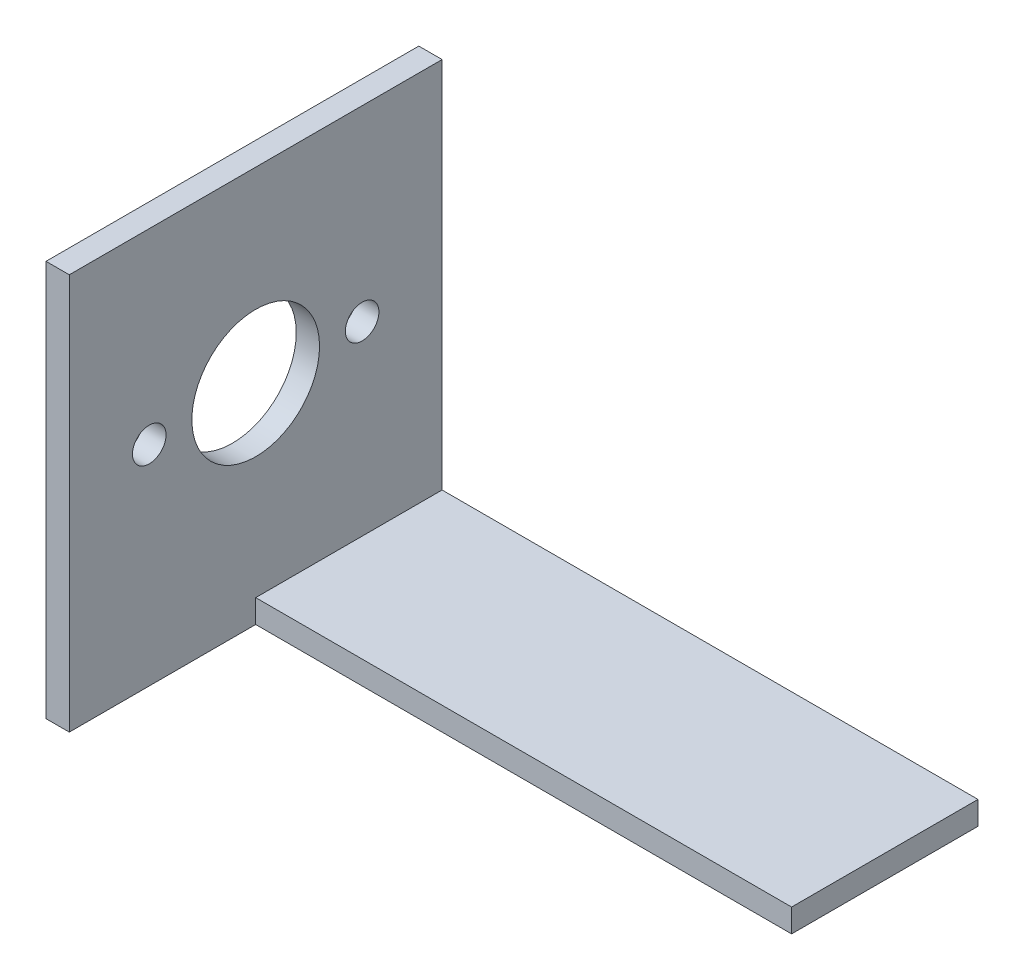
SolidWorks part; units mm, degrees
ref_plane "Front Plane" through (0, 0, 0) normal (0, 0, 1) x (1, 0, 0)
ref_plane "Top Plane" through (0, 0, 0) normal (0, 1, 0) x (1, 0, 0)
ref_plane "Right Plane" through (0, 0, 0) normal (1, 0, 0) x (0, 0, -1)
sketch "Sketch1" plane through (0, 0, 0) normal (0, 1, 0) x (1, 0, 0)
  line L1 (0, 0) -> (76.2, 0)
  line L2 (0, 0) -> (0, 50.8)
  line L3 (0, 50.8) -> (76.2, 50.8)
  line L4 (76.2, 0) -> (76.2, 50.8)
  dimension "D1" = 50.8
  dimension "D2" = 76.2
extrude "Boss-Extrude1" add sketch "Sketch1" along normal blind 3.175
sketch "Sketch2" plane through (0, 0, 0) normal (-1, 0, 0) x (0, 0, 1)
  line L0 (0, 3.175) -> (0, 0) construction
  line L1 (-50.8, 0) -> (0, 0)
  line L2 (-50.8, 0) -> (-50.8, 53.975)
  line L3 (-50.8, 53.975) -> (0, 53.975)
  line L4 (0, 0) -> (0, 53.975)
  dimension "D1" = 53.975
extrude "Boss-Extrude2" add sketch "Sketch2" against normal blind 3.175
sketch "Sketch4" plane through (3.175, 0, 0) normal (1, 0, 0) x (0, 0, -1)
  line L0 (25.4, 53.975) -> (25.4, 3.175) construction
  line L1 (0, 53.975) -> (50.8, 53.975) construction
  line L2 (50.8, 3.175) -> (0, 3.175) construction
  line L3 (0, 3.175) -> (50.8, 3.175) construction
  circle A0 centre (10.8966, 28.4988) radius 2.286
  circle A1 centre (39.9034, 28.4988) radius 2.286
  circle A2 centre (25.4, 28.4988) radius 8.6995
  dimension "D2" = 4.572
  dimension "D4" = 17.399
  dimension "D1" = 29.0068
  dimension "D3" = 25.3238
extrude "Cut-Extrude2" cut sketch "Sketch4" against normal blind 3.175
sketch "Sketch6" plane through (0, 3.175, 0) normal (0, 1, 0) x (1, 0, 0)
  line L0 (76.2, 0) -> (76.2, 50.8) construction
  line L1 (3.175, 0) -> (76.2, 0)
  line L2 (3.175, 0) -> (3.175, 25.4)
  line L3 (3.175, 25.4) -> (76.2, 25.4)
  line L4 (76.2, 0) -> (76.2, 25.4)
extrude "Cut-Extrude3" cut sketch "Sketch6" against normal blind 3.175
